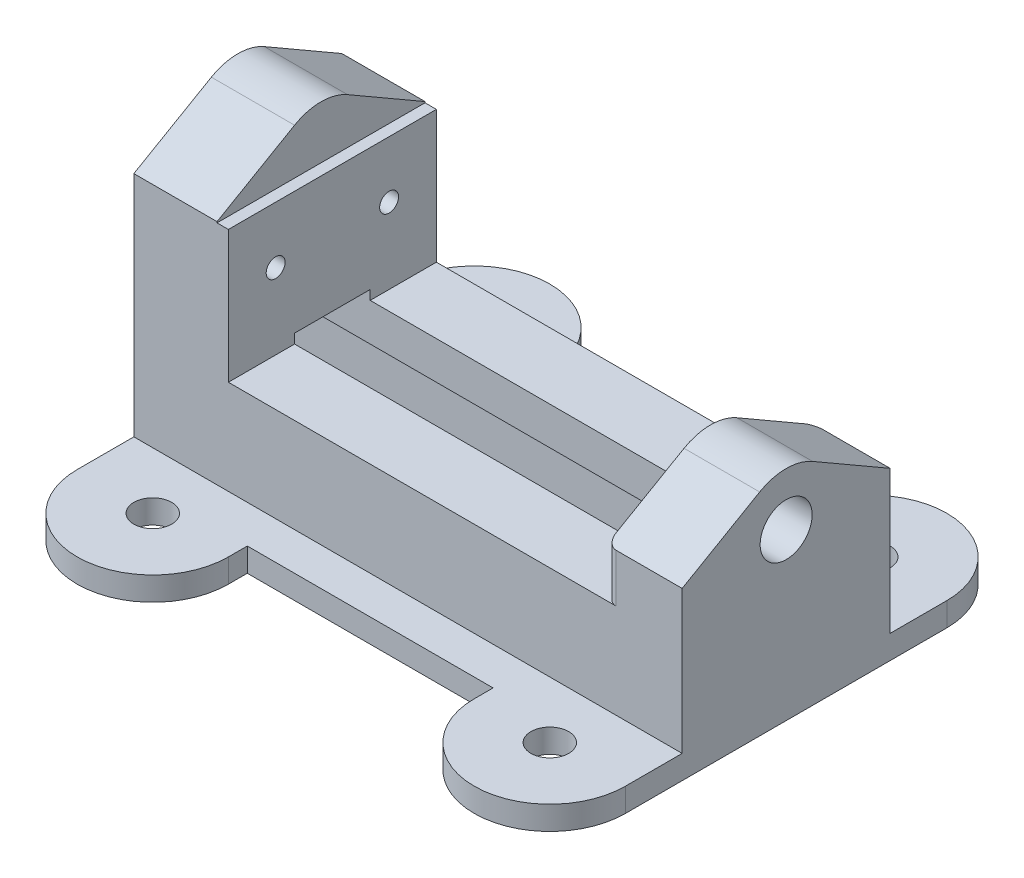
SolidWorks part; units mm, degrees
ref_plane "Front Plane" through (0, 0, 0) normal (0, 0, 1) x (1, 0, 0)
ref_plane "Top Plane" through (0, 0, 0) normal (0, 1, 0) x (1, 0, 0)
ref_plane "Right Plane" through (0, 0, 0) normal (1, 0, 0) x (0, 0, -1)
sketch "Sketch1" plane through (0, 0, 0) normal (0, 0, 1) x (1, 0, 0)
  line L1 (0, 0) -> (184.15, 0)
  line L2 (0, 0) -> (0, 39.6875)
  line L3 (0, 39.6875) -> (184.15, 39.6875)
  line L4 (184.15, 0) -> (184.15, 39.6875)
  dimension "D1" = 39.6875
  dimension "D2" = 184.15
extrude "Extrude1" add sketch "Sketch1" along normal mid plane 69.85
sketch "Sketch2" plane through (0, 0, 34.925) normal (0, 0, 1) x (1, 0, 0)
  line L1 (0, 39.6875) -> (31.75, 39.6875)
  line L2 (0, 39.6875) -> (0, 84.1375)
  line L3 (0, 84.1375) -> (31.75, 84.1375)
  line L4 (31.75, 39.6875) -> (31.75, 84.1375)
  dimension "D1" = 31.75
  dimension "D3" = 44.45
extrude "Extrude2" add sketch "Sketch2" against normal up to vertex (69.85 mm away) up to point (184.15, 39.6875, -34.925)
sketch "Sketch3" plane through (184.15, 0, 0) normal (1, 0, 0) x (0, 0, -1)
  line L0 (-34.925, 0) -> (-34.925, 39.6875) construction
  line L1 (-34.925, 39.6875) -> (34.925, 39.6875)
  line L2 (-34.925, 39.6875) -> (-34.925, 55.9291)
  line L4 (34.925, 39.6875) -> (34.925, 55.9291)
  line L5 (-34.925, 39.6875) -> (34.925, 39.6875) construction
  line L8 (0, 50) -> (0, -50) construction
  line L9 (-8.89, 70.9604) -> (-34.925, 55.9291)
  line L10 (8.89, 70.9604) -> (34.925, 55.9291)
  arc A0 (8.89, 70.9604) -> (-8.89, 70.9604) centre (0, 55.5625) ccw
  dimension "D2" = 17.78
extrude "Extrude3" add sketch "Sketch3" against normal blind 25.4
sketch "Sketch4" plane through (184.15, 0, 0) normal (1, 0, 0) x (0, 0, -1)
  line L0 (-34.925, 0) -> (34.925, 0) construction
  line L1 (-15.875, 0) -> (15.875, 0)
  line L2 (-12.7, 26.9875) -> (-12.7, 42.8625)
  line L3 (-12.7, 42.8625) -> (12.7, 42.8625)
  line L4 (12.7, 26.9875) -> (12.7, 42.8625)
  line L5 (-15.875, 0) -> (-15.875, 26.9875)
  line L6 (-15.875, 26.9875) -> (-12.7, 26.9875)
  line L7 (15.875, 26.9875) -> (15.875, 0)
  line L8 (0, 0) -> (0, 42.8625) construction
  line L9 (12.7, 26.9875) -> (15.875, 26.9875)
  dimension "D1" = 42.8625
  dimension "D2" = 25.4
  dimension "D3" = 31.75
  dimension "D4" = 26.9875
extrude "Cut-Extrude1" cut sketch "Sketch4" against normal through all from offset 15.24 offset against normal yes
sketch "Sketch5" plane through (0, 0, 0) normal (0, -1, 0) x (1, 0, 0)
  line L1 (50.8, 53.975) -> (50.8, 34.925)
  line L2 (0, 34.925) -> (0, 53.975)
  line L3 (31.75, 34.925) -> (0, 34.925) construction
  line L4 (50.8, 34.925) -> (0, 34.925)
  arc A0 (0, 53.975) -> (50.8, 53.975) centre (25.4, 53.975) cw
  dimension "D1" = 25.4
  dimension "D2" = 19.05
extrude "Extrude4" add sketch "Sketch5" against normal blind 7.9375
sketch "Sketch6" plane through (0, 0, 0) normal (0, -1, 0) x (1, 0, 0)
  line L0 (184.15, 34.925) -> (133.35, 34.925)
  line L3 (158.75, 34.925) -> (31.75, 34.925) construction
  line L4 (133.35, 34.925) -> (133.35, 53.975)
  line L6 (184.15, 34.925) -> (184.15, 53.975)
  line L7 (50.8, 34.925) -> (50.8, 53.975) construction
  arc A0 (184.15, 53.975) -> (133.35, 53.975) centre (158.75, 53.975) ccw
  arc A1 (50.8, 53.975) -> (0, 53.975) centre (25.4, 53.975) ccw construction
extrude "Extrude5" add sketch "Sketch6" against normal blind 7.9375
sketch "Sketch17" plane through (0, 0, 0) normal (0, -1, 0) x (1, 0, 0)
  line L0 (133.35, 53.975) -> (133.35, 34.925) construction
  line L1 (50.8, 34.925) -> (133.35, 34.925)
  line L2 (50.8, 34.925) -> (50.8, 47.625)
  line L3 (50.8, 47.625) -> (133.35, 47.625)
  line L4 (133.35, 34.925) -> (133.35, 47.625)
  dimension "D1" = 12.7
extrude "Extrude7" add sketch "Sketch17" against normal up to surface (7.9375 mm away) up to face at (19.05, 7.9375, 53.1812)
hole_wizard "1/2 (0.5) Diameter Hole1" positions "Sketch11" profile "Sketch10" hole size "1/2" standard "Ansi Inch" end condition through all
sketch "Sketch11" plane through (0, 7.9375, 0) normal (0, 1, 0) x (-1, 0, 0)
  line L0 (0, 0) -> (-84.8783, 0) construction
  arc A0 (0, 53.975) -> (-50.8, 53.975) centre (-25.4, 53.975) ccw construction
  point P0 (-25.4, 53.975)
  point P1 (-158.75, 53.975)
sketch "Sketch10" plane through (25.4, 7.9375, 53.975) normal (1, 0, 0) x (0, 0, 1)
  line L0 (0, 0) -> (0, 7.9375)
  line L1 (0, 7.9375) -> (6.35, 7.9375)
  line L2 (6.35, 7.9375) -> (6.35, 0)
  line L5 (6.35, 0) -> (0, 0)
  line L11 (0, -6.35) -> (0, 107.95) construction
  dimension "Thru Hole Dia." = 12.7
  dimension "Thru Hole Depth" = 7.9375
mirror "Mirror1" about plane through (0, 0, 0) normal (0, 0, 1) of "Extrude7", "Extrude5", "Extrude4", "1/2 (0.5) Diameter Hole1"
sketch "Sketch16" plane through (0, 0, 0) normal (1, 0, 0) x (0, 0, -1)
  line L0 (-34.925, 84.1375) -> (34.925, 84.1375)
  line L1 (34.925, 84.1375) -> (34.925, 84.5041)
  line L2 (-8.89, 70.9604) -> (-34.925, 55.9291) construction
  line L4 (-34.925, 84.5041) -> (-34.925, 84.1375)
  line L5 (-8.89, 99.5354) -> (-34.925, 84.5041)
  line L6 (8.89, 99.5354) -> (34.925, 84.5041)
  arc A0 (8.89, 99.5354) -> (-8.89, 99.5354) centre (0, 84.1375) ccw
  dimension "D1" = 17.78
extrude "Extrude6" add sketch "Sketch16" along normal blind 27.94
hole_wizard "1/4 (0.25) Diameter Hole2" positions "Sketch15" profile "Sketch14" hole size "1/4" standard "Ansi Inch"
sketch "Sketch15" plane through (31.75, 0, 0) normal (1, 0, 0) x (0, 0, -1)
  line L0 (0, 42.8625) -> (0, 84.1375) construction
  line L1 (12.7, 42.8625) -> (-12.7, 42.8625) construction
  line L2 (34.925, 84.1375) -> (-34.925, 84.1375) construction
  line L3 (34.925, 39.6875) -> (12.7, 39.6875) construction
  point P0 (-19.05, 65.0875)
  point P1 (19.05, 65.0875)
  dimension "D1" = 38.1
  dimension "D2" = 25.4
sketch "Sketch14" plane through (31.75, 65.0875, 19.05) normal (0, 1, 0) x (0, 0, -1)
  line L0 (0, 0) -> (0, 17.7827)
  line L1 (0, 17.7827) -> (3.175, 15.875)
  line L2 (3.175, 15.875) -> (3.175, 0)
  line L5 (3.175, 0) -> (0, 0)
  line L10 (0, 17.7827) -> (-3.175, 15.875) construction
  line L11 (0, -6.35) -> (0, 107.95) construction
  dimension "Hole Dia." = 6.35
  dimension "Hole Depth" = 15.875
  dimension "Drill Angle" = 118
hole_wizard "11/16 (0.6875) Diameter Hole1" positions "Sketch8" profile "Sketch9" hole size "11/16" standard "Ansi Inch" end condition up to next
sketch "Sketch8" plane through (184.15, 0, 0) normal (1, 0, 0) x (0, 0, -1)
  point P0 (0, 55.5625)
sketch "Sketch9" plane through (184.15, 55.5625, 0) normal (0, 1, 0) x (0, 0, -1)
  line L0 (0, 0) -> (0, 25.4)
  line L1 (0, 25.4) -> (8.7312, 25.4)
  line L2 (8.7312, 25.4) -> (8.7312, 0)
  line L5 (8.7312, 0) -> (0, 0)
  line L11 (0, -6.35) -> (0, 107.95) construction
  dimension "Thru Hole Dia." = 17.4625
  dimension "Thru Hole Depth" = 25.4
fillet "Fillet15" radius 3.175 2 edges at (158.75, 47.8083, -34.925) (158.75, 47.8083, 34.925)
